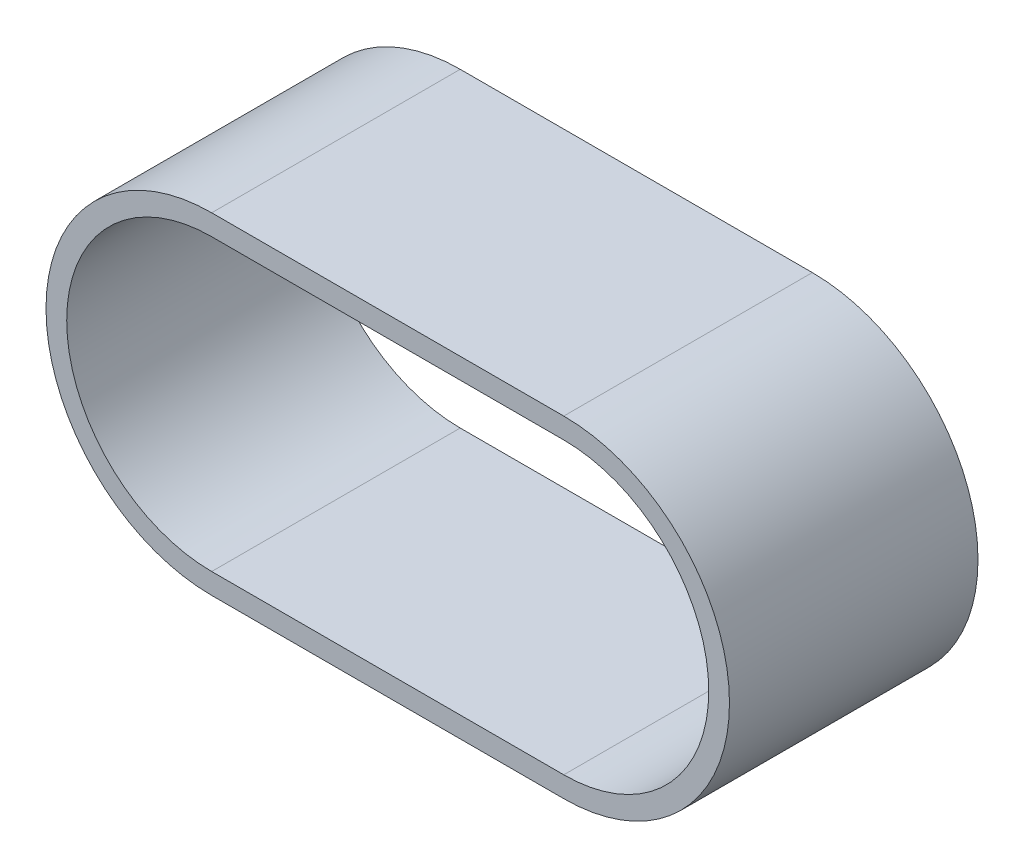
SolidWorks part; units mm, degrees
ref_plane "Plan de face" through (0, 0, 0) normal (0, 0, 1) x (1, 0, 0)
ref_plane "Plan de dessus" through (0, 0, 0) normal (0, 1, 0) x (1, 0, 0)
ref_plane "Plan de droite" through (0, 0, 0) normal (1, 0, 0) x (0, 0, -1)
sketch "Esquisse1" plane through (0, 0, 0) normal (0, 0, 1) x (1, 0, 0)
  line L0 (-62.038, 0) -> (150.8582, 0) construction
  line L1 (0, 40) -> (85, 40)
  line L2 (0, -40) -> (85, -40)
  line L3 (0, 35) -> (85, 35)
  line L4 (0, -35) -> (85, -35)
  arc A0 (0, 35) -> (0, -35) centre (0, 0) ccw
  arc A1 (85, -35) -> (85, 35) centre (85, 0) ccw
  arc A2 (0, 40) -> (0, -40) centre (0, 0) ccw
  arc A3 (85, -40) -> (85, 40) centre (85, 0) ccw
  dimension "D1" = 70
  dimension "D2" = 70
  dimension "D4" = 80
  dimension "D5" = 80
  dimension "D3" = 85
extrude "Boss.-Extru.1" add sketch "Esquisse1" along normal blind 60
